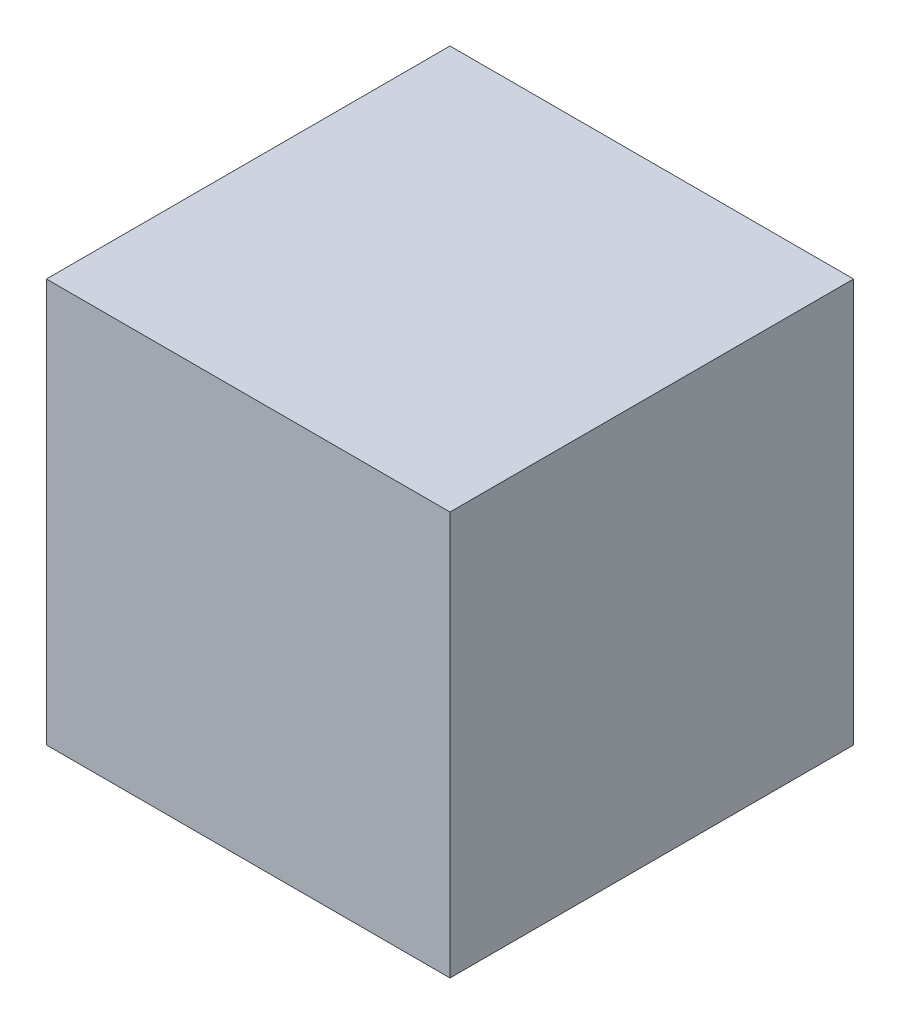
SolidWorks part; units mm, degrees
material "Beech"
ref_plane "Plane1" through (0, 0, 0) normal (0, 0, 1) x (1, 0, 0)
ref_plane "Plane2" through (0, 0, 0) normal (0, 1, 0) x (1, 0, 0)
ref_plane "Plane3" through (0, 0, 0) normal (1, 0, 0) x (0, 0, -1)
sketch "Sketch1" plane through (0, 0, 0) normal (0, 1, 0) x (1, 0, 0)
  line L1 (0, 0) -> (50, 0)
  line L2 (0, 0) -> (0, 50)
  line L3 (0, 50) -> (50, 50)
  line L4 (50, 0) -> (50, 50)
  dimension "D1" = 50
  dimension "D2" = 50
extrude "Boss-Extrude1" add sketch "Sketch1" along normal blind 50
